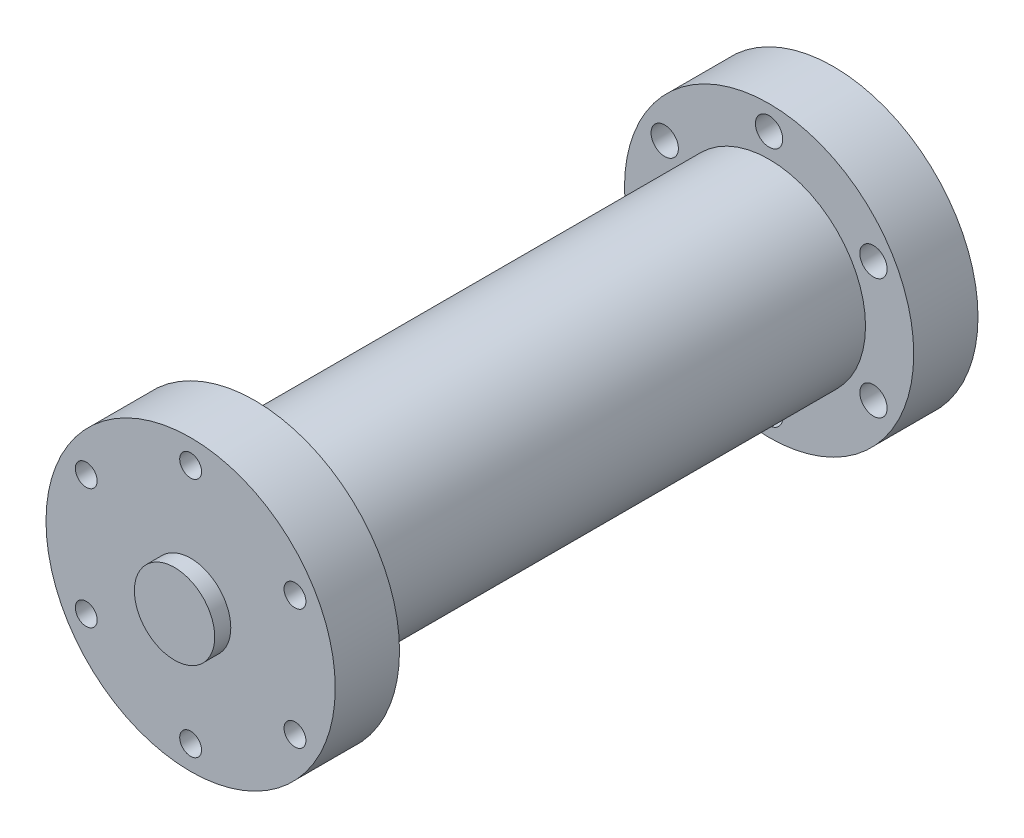
SolidWorks part; units mm, degrees
ref_plane "Plan de face" through (0, 0, 0) normal (0, 0, 1) x (1, 0, 0)
ref_plane "Plan de dessus" through (0, 0, 0) normal (0, 1, 0) x (1, 0, 0)
ref_plane "Plan de droite" through (0, 0, 0) normal (1, 0, 0) x (0, 0, -1)
sketch "Sketch1" plane through (0, 0, 0) normal (0, 0, 1) x (1, 0, 0)
  circle A0 centre (0, 0) radius 45
  dimension "D1" = 90
extrude "Boss-Extrude1" add sketch "Sketch1" along normal blind 20 contours A0
sketch "Sketch2" plane through (0, 0, 0) normal (0, 0, -1) x (-1, 0, 0)
  circle A0 centre (0, 0) radius 30
  dimension "D1" = 60
extrude "Boss-Extrude2" add sketch "Sketch2" along normal blind 160
sketch "Sketch3" plane through (0, 0, -160) normal (0, 0, -1) x (-1, 0, 0)
  circle A0 centre (0, 0) radius 45
  dimension "D1" = 90
extrude "Boss-Extrude3" add sketch "Sketch3" along normal blind 20
sketch "Sketch4" plane through (0, 0, 20) normal (0, 0, 1) x (1, 0, 0)
  circle A0 centre (0, 0) radius 12.5
  dimension "D1" = 25
extrude "Boss-Extrude4" add sketch "Sketch4" along normal blind 5
sketch "Sketch5" plane through (0, 0, 20) normal (0, 0, 1) x (1, 0, 0)
  circle A0 centre (0, 0) radius 37.5 construction
  dimension "D1" = 75
hole_wizard "M8x1.25 Tapped Hole1" positions "Sketch6" profile "Sketch7" tap size "M8x1.25" standard "ANSI Metric"
sketch "Sketch6" plane through (0, 0, 20) normal (0, 0, 1) x (1, 0, 0)
  circle A0 centre (0, 0) radius 37.5 construction
  point P0 (0, 37.5)
sketch "Sketch7" plane through (0, 37.5, 20) normal (1, 0, 0) x (0, -1, 0)
  line L0 (0, 0) -> (0, 200)
  line L1 (0, 200) -> (3.4, 200)
  line L2 (3.4, 200) -> (3.4, 0)
  line L5 (3.4, 0) -> (0, 0)
  line L11 (0, -6.35) -> (0, 107.95) construction
  dimension "Thread Major Dia." = 6.8
  dimension "Thru Tap Drill Depth" = 200
pattern_circular "CirPattern1" count 6 over 360 about axis through (0, 0, 0) along (0, 0, 1) of "M8x1.25 Tapped Hole1"
sketch "Sketch8" plane through (0, 0, -180) normal (0, 0, -1) x (-1, 0, 0)
  circle A0 centre (0, 0) radius 37.5 construction
  dimension "D1" = 75
hole_wizard "Ø8.5 (8.5) Diameter Hole1" positions "Sketch9" profile "Sketch10" hole size "Ø8.5" standard "ANSI Metric" end condition up to next
sketch "Sketch9" plane through (0, 0, -180) normal (0, 0, -1) x (-1, 0, 0)
  circle A0 centre (0, 0) radius 37.5 construction
  point P0 (0, 37.5)
sketch "Sketch10" plane through (0, 37.5, -180) normal (1, 0, 0) x (0, 1, 0)
  line L0 (0, 0) -> (0, 20.001)
  line L1 (0, 20.001) -> (4.25, 20.001)
  line L2 (4.25, 20.001) -> (4.25, 0)
  line L5 (4.25, 0) -> (0, 0)
  line L11 (0, -6.35) -> (0, 107.95) construction
  dimension "Thru Hole Dia." = 8.5
  dimension "Thru Hole Depth" = 20.001
pattern_circular "CirPattern2" count 6 over 360 about axis through (0, 0, 0) along (0, 0, 1) of "Ø8.5 (8.5) Diameter Hole1"
sketch "Sketch11" plane through (0, 0, -180) normal (0, 0, -1) x (-1, 0, 0)
  circle A0 centre (0, 0) radius 12.5
  dimension "D1" = 25
extrude "Cut-Extrude1" cut sketch "Sketch11" against normal blind 60
